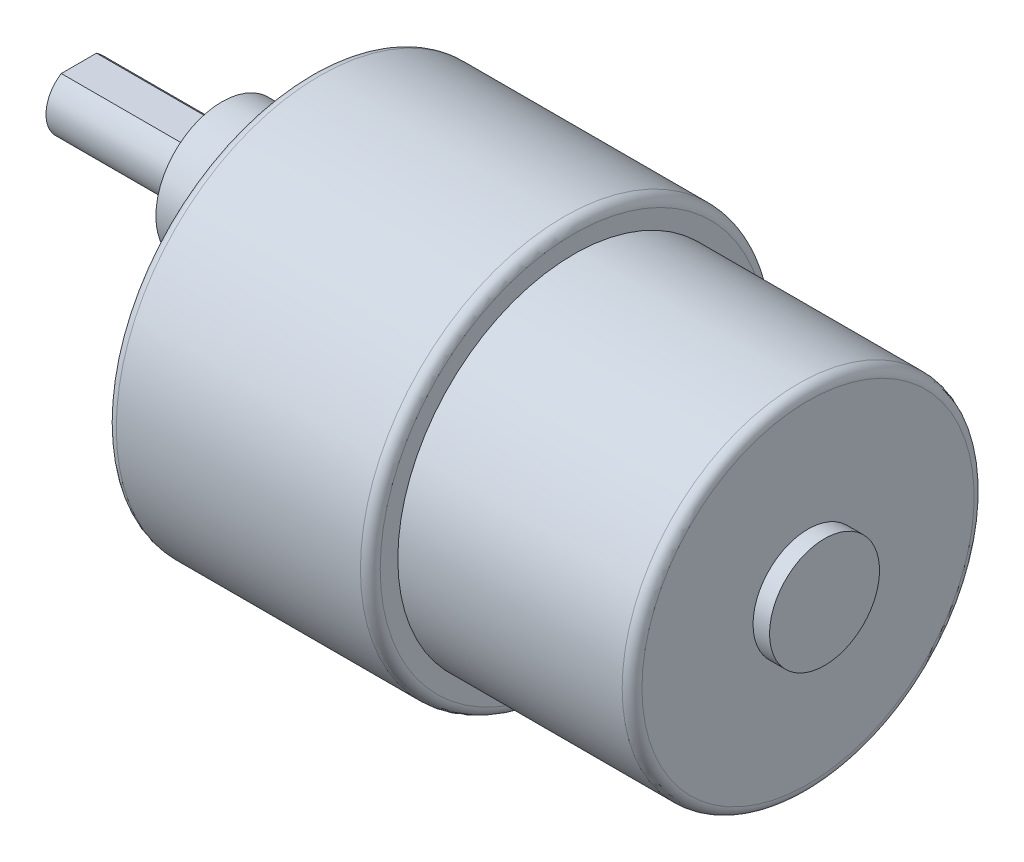
SolidWorks part; units mm, degrees
ref_plane "Front Plane" through (0, 0, 0) normal (0, 0, 1) x (1, 0, 0)
ref_plane "Top Plane" through (0, 0, 0) normal (0, 1, 0) x (1, 0, 0)
ref_plane "Right Plane" through (0, 0, 0) normal (1, 0, 0) x (0, 0, -1)
sketch "Sketch1" plane through (0, 0, 0) normal (0, 1, 0) x (1, 0, 0)
  line L0 (-35.5467, 0) -> (38.6986, 0) construction
  line L1 (-23.3, 0) -> (23.5, 0)
  line L2 (0.7, 16) -> (21.1, 16)
  line L3 (22, 15.1) -> (22, 5)
  line L4 (-23.3, 0) -> (-23.3, 17.6)
  line L5 (-22.4, 18.5) -> (-0.2, 18.5)
  line L6 (0.7, 17.6) -> (0.7, 16)
  line L7 (22, 5) -> (23.5, 5)
  line L8 (23.5, 5) -> (23.5, 0)
  arc A0 (21.1, 16) -> (22, 15.1) centre (21.1, 15.1) cw
  arc A1 (-0.2, 18.5) -> (0.7, 17.6) centre (-0.2, 17.6) cw
  arc A2 (-23.3, 17.6) -> (-22.4, 18.5) centre (-22.4, 17.6) cw
  point P12 (22, 16)
  point P16 (0.7, 18.5)
  point P19 (-23.3, 18.5)
  dimension "D1" = 0.9
  dimension "D2" = 21.3
  dimension "D3" = 18.5
  dimension "D4" = 24
  dimension "D5" = 1.5
  dimension "D6" = 5
revolve "Revolve2" add sketch "Sketch1" angle 360 about L0
sketch "Sketch2" plane through (-23.3, 0, 0) normal (-1, 0, 0) x (0, 0, 1)
  circle A0 centre (0, 6) radius 6
  dimension "D1" = 12
extrude "Boss-Extrude1" add sketch "Sketch2" along normal blind 8
sketch "Sketch3" plane through (-31.3, 0, 0) normal (-1, 0, 0) x (0, 0, 1)
  circle A0 centre (0, 6) radius 2.9904
  circle A1 centre (0, 6) radius 6 construction
extrude "Boss-Extrude2" add sketch "Sketch3" along normal blind 13
sketch "Sketch5" plane through (-44.3, 0, 0) normal (-1, 0, 0) x (0, 0, 1)
  line L0 (-1.6, 8.5264) -> (1.6, 8.5264)
  circle A0 centre (0, 6) radius 2.9904 construction
  arc A1 (1.6, 8.5264) -> (-1.6, 8.5264) centre (0, 6) ccw
extrude "Cut-Extrude1" cut sketch "Sketch5" against normal blind 11
sketch "Sketch6" plane through (-23.3, 0, 0) normal (-1, 0, 0) x (0, 0, 1)
  arc A0 (-7.1102, 9.6667) -> (7.1102, 9.6667) centre (0, 6) ccw
  arc A1 (-7.1102, 9.6667) -> (7.1102, 9.6667) centre (0, 0) ccw
  dimension "D1" = 16
  dimension "D2" = 24
extrude "Cut-Extrude2" cut sketch "Sketch6" against normal blind 1
sketch "Sketch7" plane through (-23.3, 0, 0) normal (-1, 0, 0) x (0, 0, 1)
  line L0 (-24.4963, 0) -> (25.0441, 0) construction
  line L1 (0, 24.9169) -> (0, -24.6966) construction
  circle A0 centre (15.5, 0) radius 0.75
  circle A1 centre (0, 0) radius 17.6 construction
  dimension "D2" = 1.5
  dimension "D1" = 15.5
extrude "Cut-Extrude4" cut sketch "Sketch7" against normal blind 2
pattern_circular "CirPattern1" count 6 over 360 about axis through (0, 0, 0) along (1, 0, 0) of "Cut-Extrude4"
